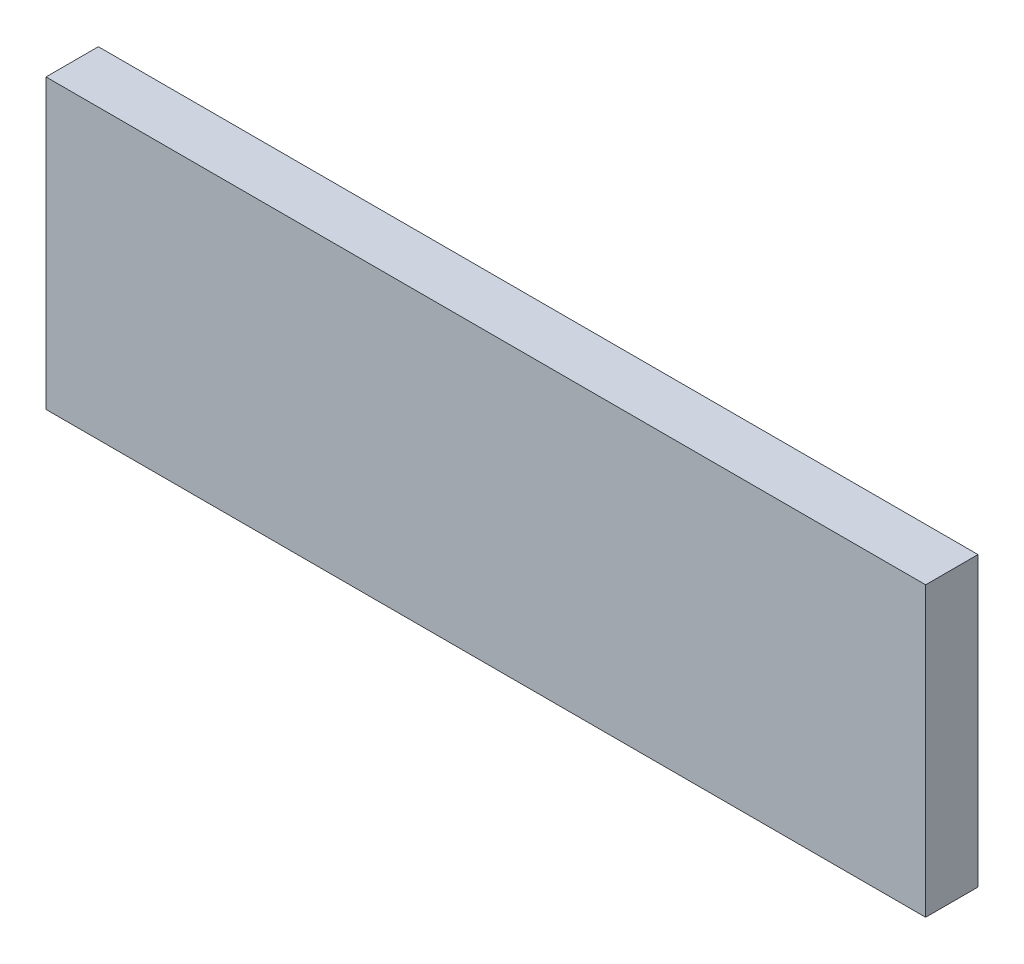
SolidWorks part; units mm, degrees
ref_plane "Plan de face" through (0, 0, 0) normal (0, 0, 1) x (1, 0, 0)
ref_plane "Plan de dessus" through (0, 0, 0) normal (0, 1, 0) x (1, 0, 0)
ref_plane "Plan de droite" through (0, 0, 0) normal (1, 0, 0) x (0, 0, -1)
sketch "Esquisse1" plane through (0, 0, 0) normal (0, 0, 1) x (1, 0, 0)
  line L1 (-88.0965, 196.7363) -> (79.9035, 196.7363)
  line L2 (-88.0965, 196.7363) -> (-88.0965, 141.7363)
  line L3 (-88.0965, 141.7363) -> (79.9035, 141.7363)
  line L4 (79.9035, 196.7363) -> (79.9035, 141.7363)
  dimension "D1" = 55
  dimension "D2" = 168
extrude "Boss.-Extru.1" add sketch "Esquisse1" along normal blind 10
